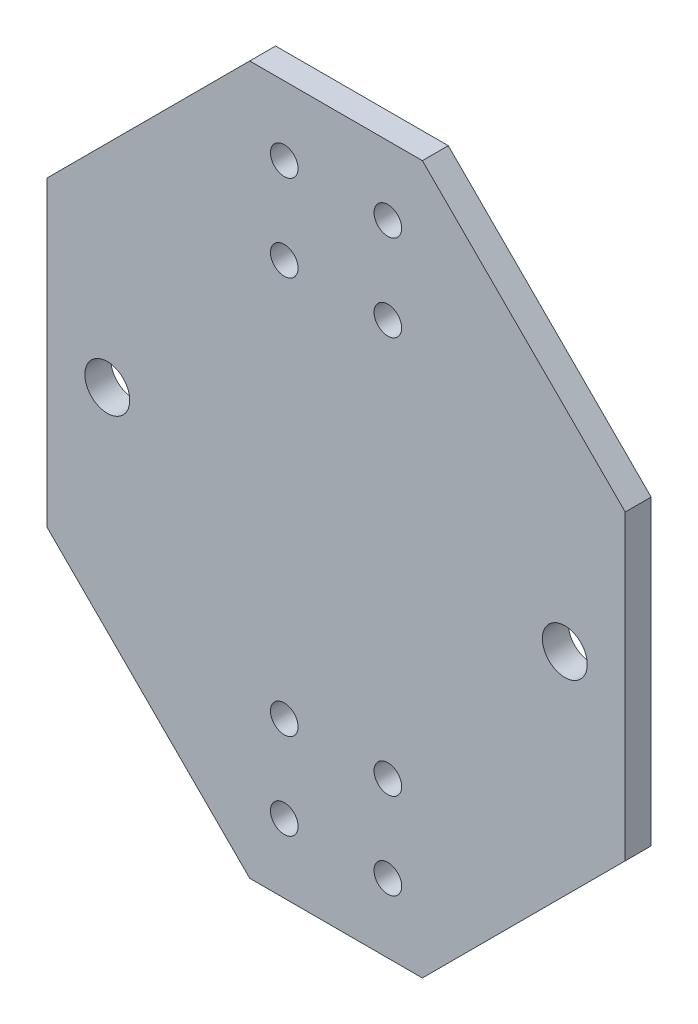
SolidWorks part; units mm, degrees
material "Thornel Mat VMA"
ref_plane "前视基准面" through (0, 0, 0) normal (0, 0, 1) x (1, 0, 0)
ref_plane "上视基准面" through (0, 0, 0) normal (0, 1, 0) x (1, 0, 0)
ref_plane "右视基准面" through (0, 0, 0) normal (1, 0, 0) x (0, 0, -1)
sketch "Sketch1" plane through (0, 0, 0) normal (0, 0, 1) x (1, 0, 0)
  line L0 (-70.0006, -293.595) -> (-50.0006, -293.595)
  line L1 (-70.0006, 147.905) -> (-70.0006, -492.095) construction
  line L2 (-50.0006, -492.095) -> (-50.0006, 147.905) construction
  line L3 (-50.0006, -293.595) -> (-26.5006, -317.095)
  line L4 (-26.5006, -317.095) -> (-26.5006, -352.095)
  line L5 (-26.5006, -352.095) -> (-50.0006, -375.595)
  line L6 (-50.0006, -375.595) -> (-70.0006, -375.595)
  line L7 (-70.0006, -375.595) -> (-93.5006, -352.095)
  line L8 (-93.5006, -352.095) -> (-93.5006, -317.095)
  line L9 (-93.5006, -317.095) -> (-70.0006, -293.595)
  line L10 (-26.5006, -329.595) -> (-26.5006, -339.595) construction
  line L11 (-29.5006, -342.595) -> (-40.8995, -342.595) construction
  line L12 (-79.1759, -326.595) -> (-90.5006, -326.595) construction
  line L14 (-66.0006, -357.595) -> (-54.0006, -357.595) construction
  line L15 (-66.0006, -357.595) -> (-66.0006, -311.595) construction
  line L16 (-66.0006, -367.595) -> (-54.0006, -367.595) construction
  line L17 (-66.0006, -367.595) -> (-66.0006, -301.595) construction
  line L18 (-66.0006, -301.595) -> (-54.0006, -301.595) construction
  line L19 (-54.0006, -367.595) -> (-54.0006, -301.595) construction
  line L20 (-66.0006, -367.595) -> (-54.0006, -301.595) construction
  line L21 (-66.0006, -301.595) -> (-54.0006, -367.595) construction
  line L22 (-66.0006, -311.595) -> (-54.0006, -311.595) construction
  line L23 (-54.0006, -357.595) -> (-54.0006, -311.595) construction
  line L24 (-66.0006, -357.595) -> (-54.0006, -311.595) construction
  line L25 (-66.0006, -311.595) -> (-54.0006, -357.595) construction
  circle A0 centre (-86.5006, -334.595) radius 2.6
  circle A1 centre (-33.5006, -334.595) radius 2.6
  circle A2 centre (-66.0006, -301.595) radius 1.6
  circle A3 centre (-54.0006, -301.595) radius 1.6
  circle A4 centre (-66.0006, -367.595) radius 1.6
  circle A5 centre (-54.0006, -367.595) radius 1.6
  circle A6 centre (-66.0006, -311.595) radius 1.6
  circle A7 centre (-54.0006, -311.595) radius 1.6
  circle A8 centre (-66.0006, -357.595) radius 1.6
  circle A9 centre (-54.0006, -357.595) radius 1.6
  point P24 (-60.0006, -334.595)
  point P33 (-60.0006, -334.595)
  dimension "D7" = 5.2
  dimension "D9" = 3.2
  dimension "D1" = 45
  dimension "D2" = 45
  dimension "D3" = 45
  dimension "D4" = 45
  dimension "D5" = 33
  dimension "D6" = 33
  dimension "D8" = 4
  dimension "D10" = 4
  dimension "D11" = 8
  dimension "D12" = 8
  dimension "D13" = 10
extrude "Boss-Extrude1" add sketch "Sketch1" along normal blind 3
